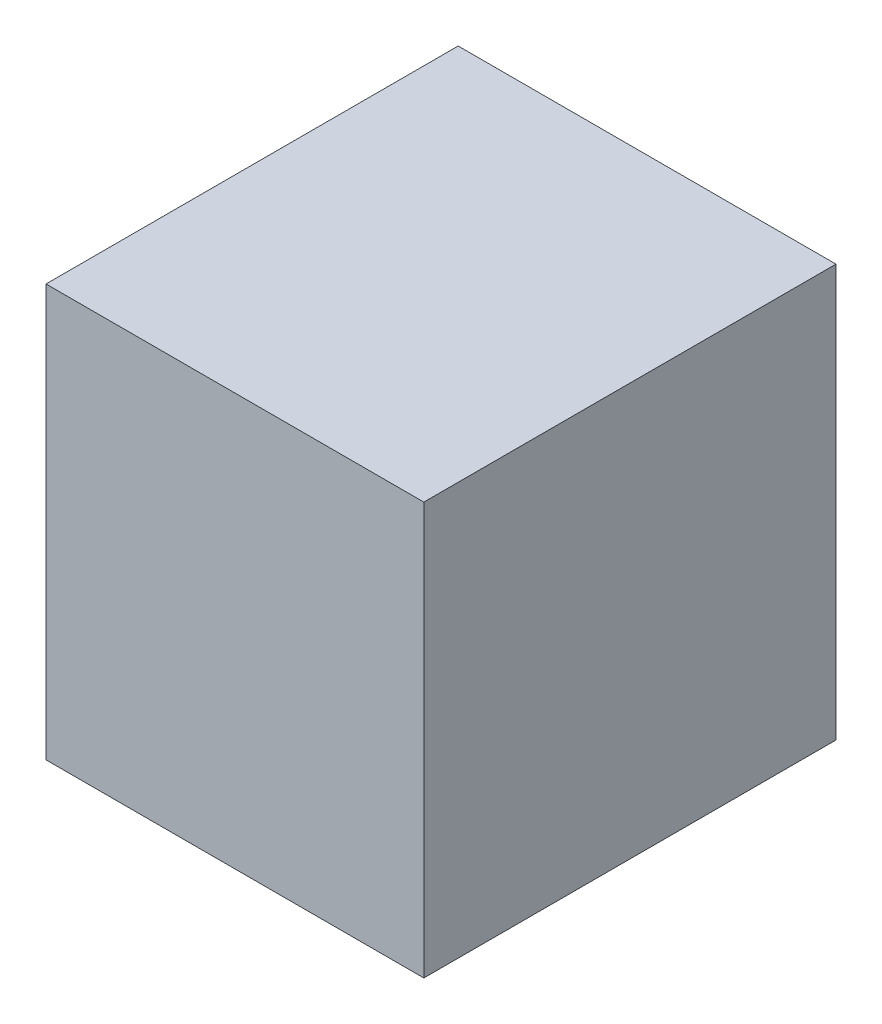
SolidWorks part; units mm, degrees
ref_plane "Front Plane" through (0, 0, 0) normal (0, 0, 1) x (1, 0, 0)
ref_plane "Top Plane" through (0, 0, 0) normal (0, 1, 0) x (1, 0, 0)
ref_plane "Right Plane" through (0, 0, 0) normal (1, 0, 0) x (0, 0, -1)
sketch "Sketch1" plane through (0, 0, 0) normal (0, 0, 1) x (1, 0, 0)
  line L1 (0, 0) -> (-550, 0)
  line L2 (0, 0) -> (0, 600)
  line L3 (0, 600) -> (-550, 600)
  line L4 (-550, 0) -> (-550, 600)
  dimension "D1" = 550
  dimension "D2" = 600
extrude "Boss-Extrude1" add sketch "Sketch1" along normal blind 600
